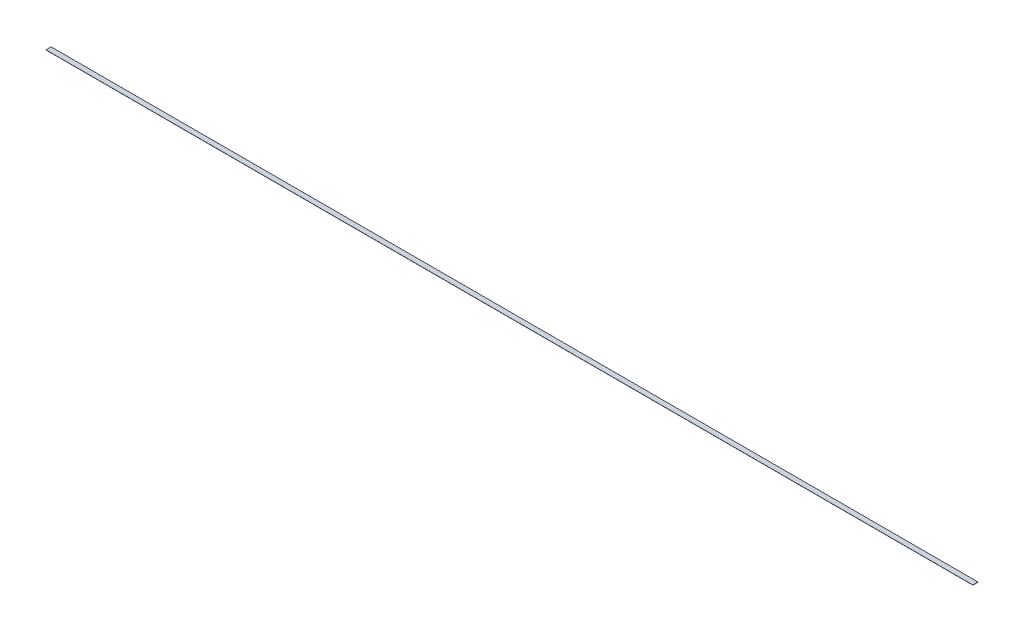
SolidWorks part; units mm, degrees
ref_plane "Front Plane" through (0, 0, 0) normal (0, 0, 1) x (1, 0, 0)
ref_plane "Top Plane" through (0, 0, 0) normal (0, 1, 0) x (1, 0, 0)
ref_plane "Right Plane" through (0, 0, 0) normal (1, 0, 0) x (0, 0, -1)
sketch "Sketch1" plane through (0, 0, 0) normal (0, 1, 0) x (1, 0, 0)
  line L1 (0, 0) -> (9144, 0)
  line L2 (0, 0) -> (0, 50.8)
  line L3 (0, 50.8) -> (9144, 50.8)
  line L4 (9144, 0) -> (9144, 50.8)
  dimension "D1" = 50.8
  dimension "D2" = 9144
extrude "Boss-Extrude1" add sketch "Sketch1" along normal blind 1.5875
